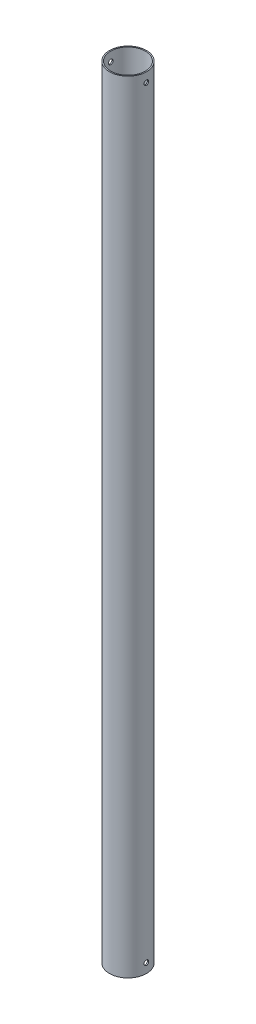
SolidWorks part; units mm, degrees
ref_plane "Front" through (0, 0, 0) normal (0, 0, 1) x (1, 0, 0)
ref_plane "Top" through (0, 0, 0) normal (0, 1, 0) x (1, 0, 0)
ref_plane "Right" through (0, 0, 0) normal (1, 0, 0) x (0, 0, -1)
sketch "Sketch2" plane through (0, 0, 0) normal (0, 1, 0) x (1, 0, 0)
  circle A0 centre (0, 0) radius 24.972
  dimension "D1" = 49.944
extrude "Extrude-Thin1" add sketch "Sketch2" along normal blind 1054.1 thin thin type one direction reverse wall 1.5875
sketch "Sketch4" plane through (0, 0, 0) normal (1, 0, 0) x (0, 0, -1)
  line L0 (0, 1054.1) -> (0, 1041.4) construction
  line L1 (24.972, 1054.1) -> (-24.972, 1054.1) construction
  circle A0 centre (0, 1041.4) radius 3.175
  dimension "D1" = 6.35
  dimension "D2" = 12.7
extrude "Cut-Extrude1" cut sketch "Sketch4" against normal through all both and the other way through all
ref_plane "Plane1" through (0, 527.05, 0) normal (0, 1, 0) x (1, 0, 0)
mirror "Mirror1" about plane through (0, 527.05, 0) normal (0, 1, 0) of "Cut-Extrude1"
